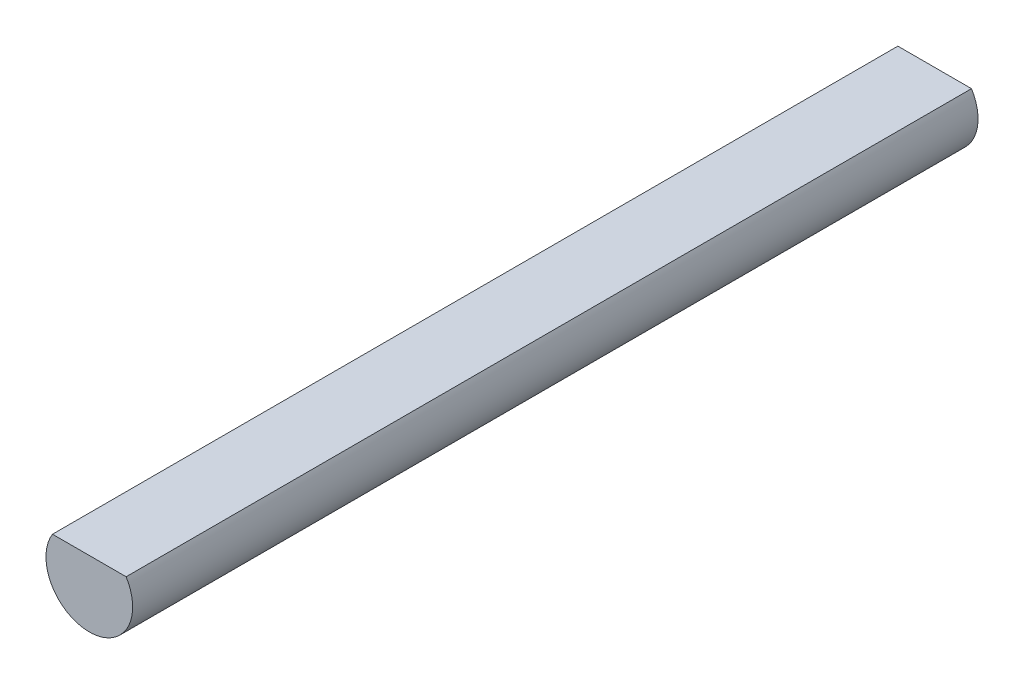
SolidWorks part; units mm, degrees
ref_plane "Front" through (0, 0, 0) normal (0, 0, 1) x (1, 0, 0)
ref_plane "Top" through (0, 0, 0) normal (0, 1, 0) x (1, 0, 0)
ref_plane "Right" through (0, 0, 0) normal (1, 0, 0) x (0, 0, -1)
sketch "Sketch1" plane through (0, 0, 0) normal (0, 0, 1) x (1, 0, 0)
  line L0 (-25, 0) -> (25, 0)
  arc A0 (-25, 0) -> (25, 0) centre (0, -15.5556) ccw
  dimension "D1" = 45
  dimension "D2" = 50
extrude "Boss-Extrude1" add sketch "Sketch1" along normal mid plane 574
